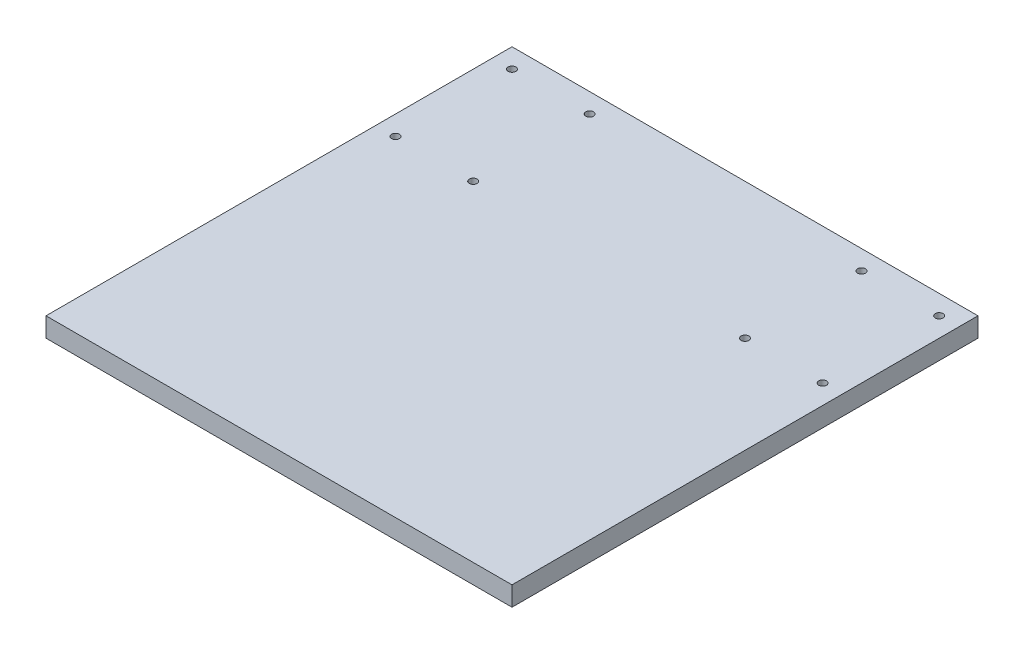
SolidWorks part; units mm, degrees
ref_plane "Plano frontal" through (0, 0, 0) normal (0, 0, 1) x (1, 0, 0)
ref_plane "Plano superior" through (0, 0, 0) normal (0, 1, 0) x (1, 0, 0)
ref_plane "Plano direito" through (0, 0, 0) normal (1, 0, 0) x (0, 0, -1)
sketch "Esboço2" plane through (0, 0, 0) normal (0, 1, 0) x (1, 0, 0)
  line L0 (0, 120) -> (0, 0) construction
  line L1 (-120, 120) -> (120, 120)
  line L2 (-120, 120) -> (-120, -120)
  line L3 (-120, -120) -> (120, -120)
  line L4 (120, 120) -> (120, -120)
  line L5 (-120, 120) -> (120, -120) construction
  line L6 (-120, -120) -> (120, 120) construction
  circle A0 centre (-110, 110) radius 2
  circle A1 centre (-110, 50) radius 2
  circle A2 centre (-70, 110) radius 2
  circle A3 centre (-70, 50) radius 2
  circle A4 centre (70, 50) radius 2
  circle A5 centre (70, 110) radius 2
  circle A6 centre (110, 50) radius 2
  circle A7 centre (110, 110) radius 2
  point P0 (0, 0)
  dimension "D2" = 4
  dimension "D1" = 240
  dimension "D3" = 60
  dimension "D4" = 10
  dimension "D5" = 10
  dimension "D7" = 40
  dimension "D6" = 2
extrude "Ressalto-extrusão1" add sketch "Esboço2" along normal blind 10
